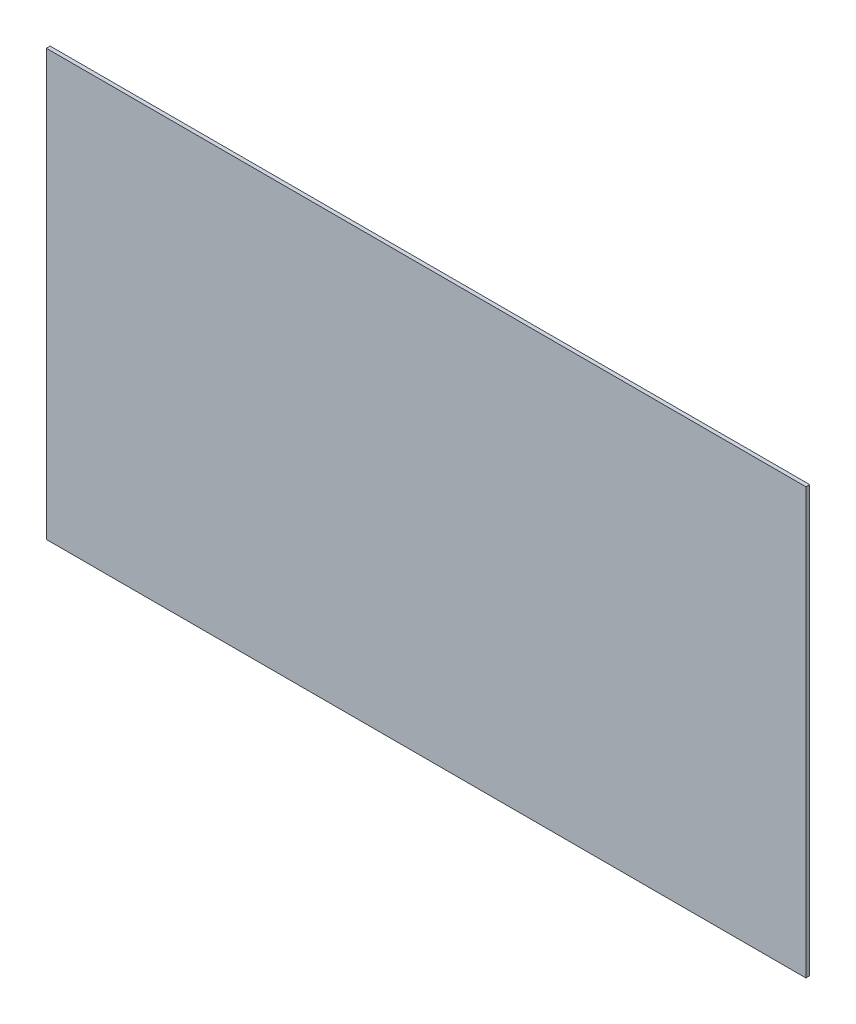
SolidWorks part; units mm, degrees
ref_plane "Ön Düzlem" through (0, 0, 0) normal (0, 0, 1) x (1, 0, 0)
ref_plane "Üst Düzlem" through (0, 0, 0) normal (0, 1, 0) x (1, 0, 0)
ref_plane "Sağ Düzlem" through (0, 0, 0) normal (1, 0, 0) x (0, 0, -1)
sketch "Çizim1" plane through (0, 0, 0) normal (0, 0, 1) x (1, 0, 0)
  line L1 (0, 0) -> (600, 0)
  line L2 (0, 0) -> (0, -336)
  line L3 (0, -336) -> (600, -336)
  line L4 (600, 0) -> (600, -336)
  dimension "D1" = 600
  dimension "D2" = 336
extrude "Yükseklik-Ekstrüzyon1" add sketch "Çizim1" along normal blind 3
